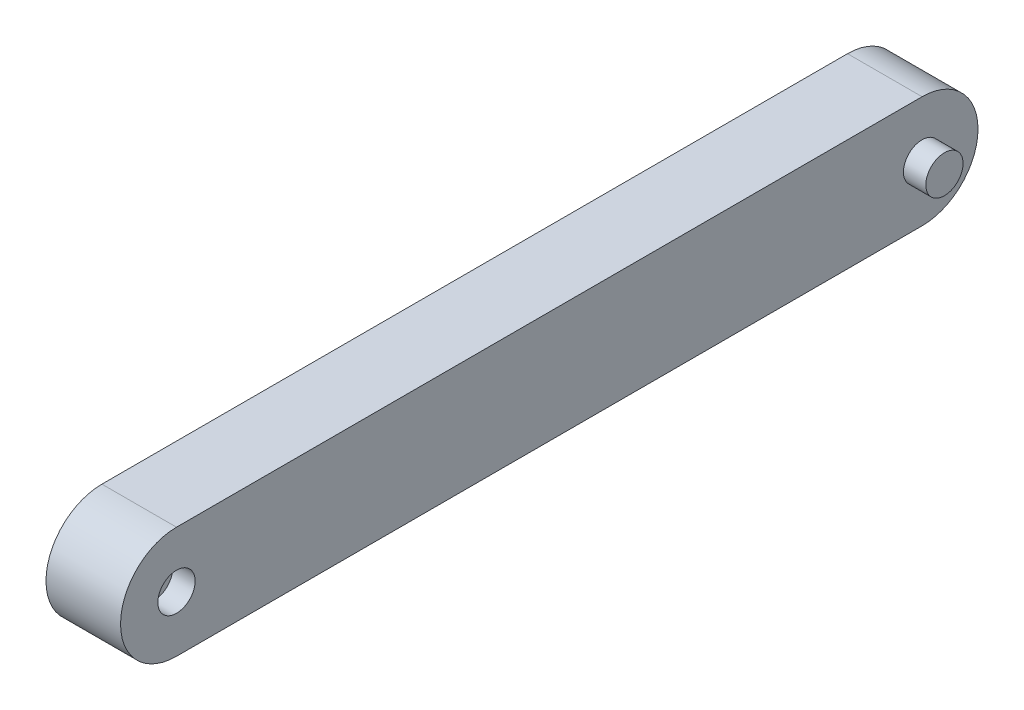
SolidWorks part; units mm, degrees
ref_plane "Front Plane" through (0, 0, 0) normal (0, 0, 1) x (1, 0, 0)
ref_plane "Top Plane" through (0, 0, 0) normal (0, 1, 0) x (1, 0, 0)
ref_plane "Right Plane" through (0, 0, 0) normal (1, 0, 0) x (0, 0, -1)
sketch "Sketch3" plane through (0, 0, 0) normal (1, 0, 0) x (0, 0, -1)
  line L1 (100, -15) -> (-100, -15)
  line L3 (100, 15) -> (-100, 15)
  line L5 (105.8603, -13.8079) -> (-105.8603, 13.8079) construction
  line L6 (105.8603, 13.8079) -> (-105.8603, -13.8079) construction
  arc A0 (-100, 15) -> (-100, -15) centre (-100, 0) ccw
  arc A1 (100, 15) -> (100, -15) centre (100, 0) cw
  point P0 (0, 0)
  dimension "D3" = 15
  dimension "D1" = 200
extrude "Boss-Extrude2" add sketch "Sketch3" along normal blind 20
sketch "Sketch4" plane through (20, 0, 0) normal (1, 0, 0) x (0, 0, -1)
  circle A0 centre (100, 0) radius 5
  arc A1 (100, -15) -> (100, 15) centre (100, 0) ccw construction
  dimension "D1" = 10
extrude "Boss-Extrude3" add sketch "Sketch4" along normal blind 6
sketch "Sketch5" plane through (20, 0, 0) normal (1, 0, 0) x (0, 0, -1)
  circle A0 centre (-100, 0) radius 5
  arc A1 (-100, 15) -> (-100, -15) centre (-100, 0) ccw construction
  dimension "D1" = 10
extrude "Cut-Extrude1" cut sketch "Sketch5" against normal blind 6
ref_plane "Plane1" through (10, 0, 0) normal (1, 0, 0) x (0, 0, -1)
mirror "Mirror1" about plane through (10, 0, 0) normal (1, 0, 0) of "Cut-Extrude1", "Boss-Extrude3"
